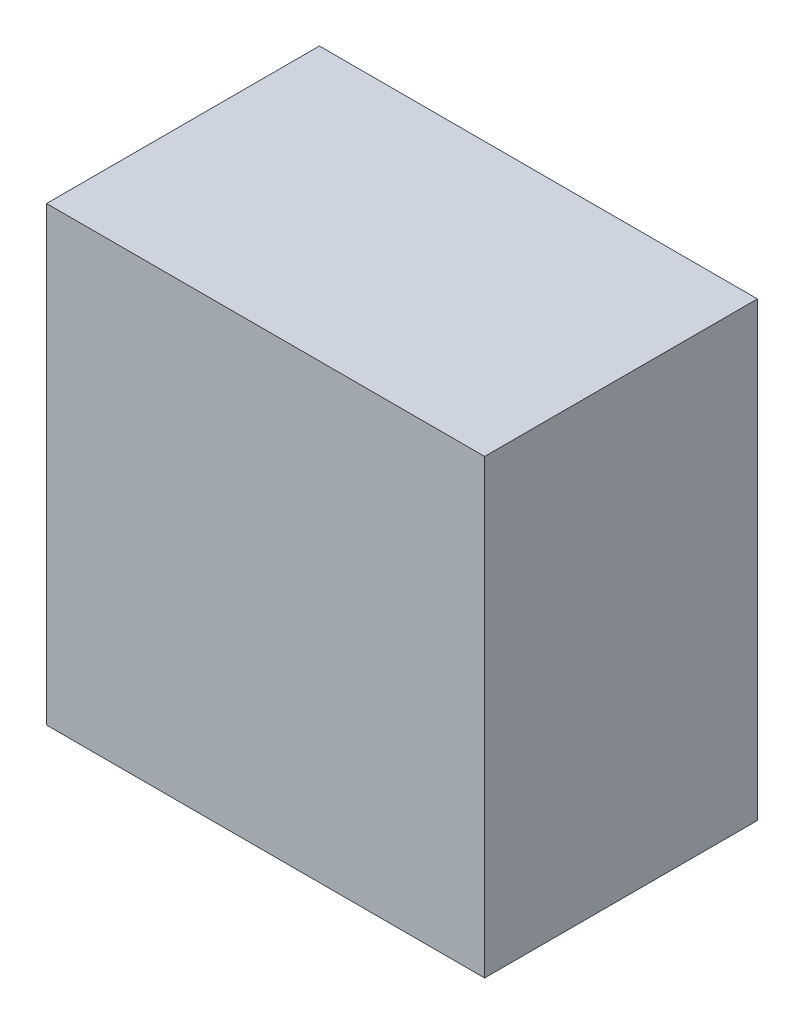
SolidWorks part; units mm, degrees
ref_plane "Front Plane" through (0, 0, 0) normal (0, 0, 1) x (1, 0, 0)
ref_plane "Top Plane" through (0, 0, 0) normal (0, 1, 0) x (1, 0, 0)
ref_plane "Right Plane" through (0, 0, 0) normal (1, 0, 0) x (0, 0, -1)
sketch "Sketch2" plane through (0, 0, 0) normal (0, 0, 1) x (1, 0, 0)
  line L1 (-72.25, 74.5) -> (72.25, 74.5)
  line L6 (-72.25, 74.5) -> (-72.25, -74.5)
  line L7 (-72.25, -74.5) -> (72.25, -74.5)
  line L8 (72.25, 74.5) -> (72.25, -74.5)
  line L9 (-72.25, 74.5) -> (72.25, -74.5) construction
  line L10 (-72.25, -74.5) -> (72.25, 74.5) construction
  point P0 (0, 0)
  dimension "D1" = 144.5
  dimension "D2" = 149
extrude "Boss-Extrude2" add sketch "Sketch2" along normal blind 90
